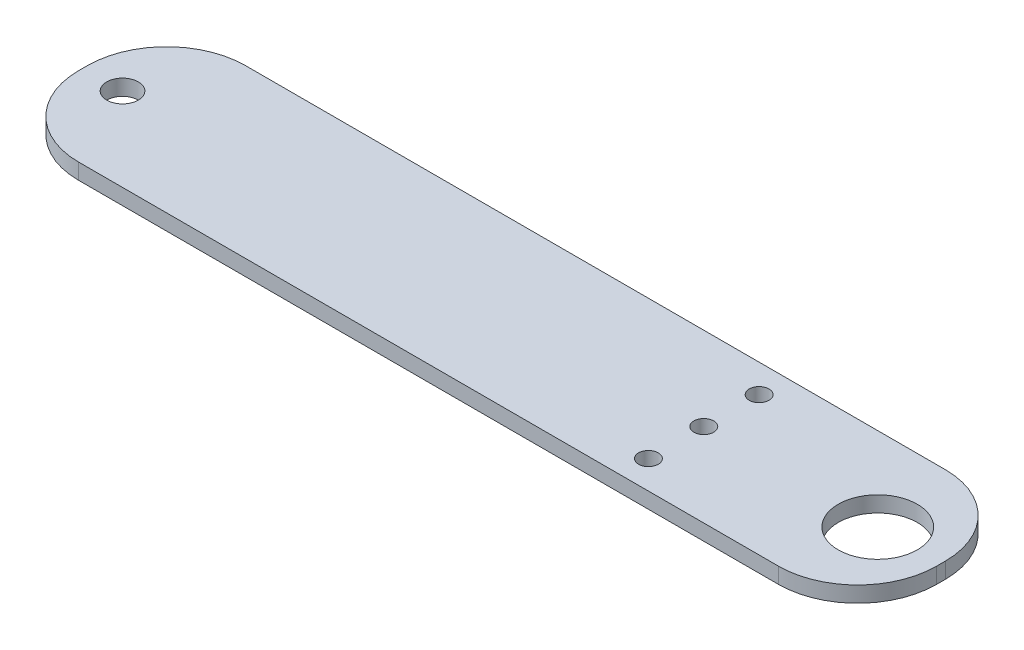
SolidWorks part; units mm, degrees
ref_plane "Front Plane" through (0, 0, 0) normal (0, 0, 1) x (1, 0, 0)
ref_plane "Top Plane" through (0, 0, 0) normal (0, 1, 0) x (1, 0, 0)
ref_plane "Right Plane" through (0, 0, 0) normal (1, 0, 0) x (0, 0, -1)
sketch "Sketch1" plane through (0, 0, 0) normal (0, 1, 0) x (1, 0, 0)
  line L0 (-62, 0) -> (62, 0) construction
  line L1 (-38.5, 10.5584) -> (70, 10.5584)
  line L2 (-70, 10.5584) -> (-70, -10.5584) construction
  line L3 (-38.5, -10.5584) -> (70, -10.5584)
  line L4 (70, 10.5584) -> (70, -10.5584)
  line L5 (-38.5, -10.5584) -> (-38.5, 10.5584)
  line L6 (-38.5, -10.5584) -> (-70, -10.5584) construction
  line L7 (-38.5, 10.5584) -> (-70, 10.5584) construction
  line L9 (-38.5, 0.5584) -> (-38.5, -0.5584) construction
  circle A0 centre (-62, 0) radius 5 construction
  circle A1 centre (62, 0) radius 5
  circle A2 centre (-33.5, 0) radius 2
  circle A3 centre (62, 0) radius 1.2099
  circle A4 centre (40, 0) radius 1.25
  circle A5 centre (40, 7) radius 1.25
  circle A6 centre (40, -7) radius 1.25
  point P6 (-70, 0)
  point P9 (0, 0)
  dimension "D3" = 10
  dimension "D4" = 4
  dimension "D5" = 2.5
  dimension "D1" = 140
  dimension "D2" = 124
extrude "Boss-Extrude1" add sketch "Sketch1" along normal blind 2 contours L5 L3 L4 L1 A4 A2 A1
fillet "Fillet1" radius 10 4 edges at (-38.5, 1, -10.5584) (-38.5, 1, 10.5584) (70, 1, 10.5584) (70, 1, -10.5584)
